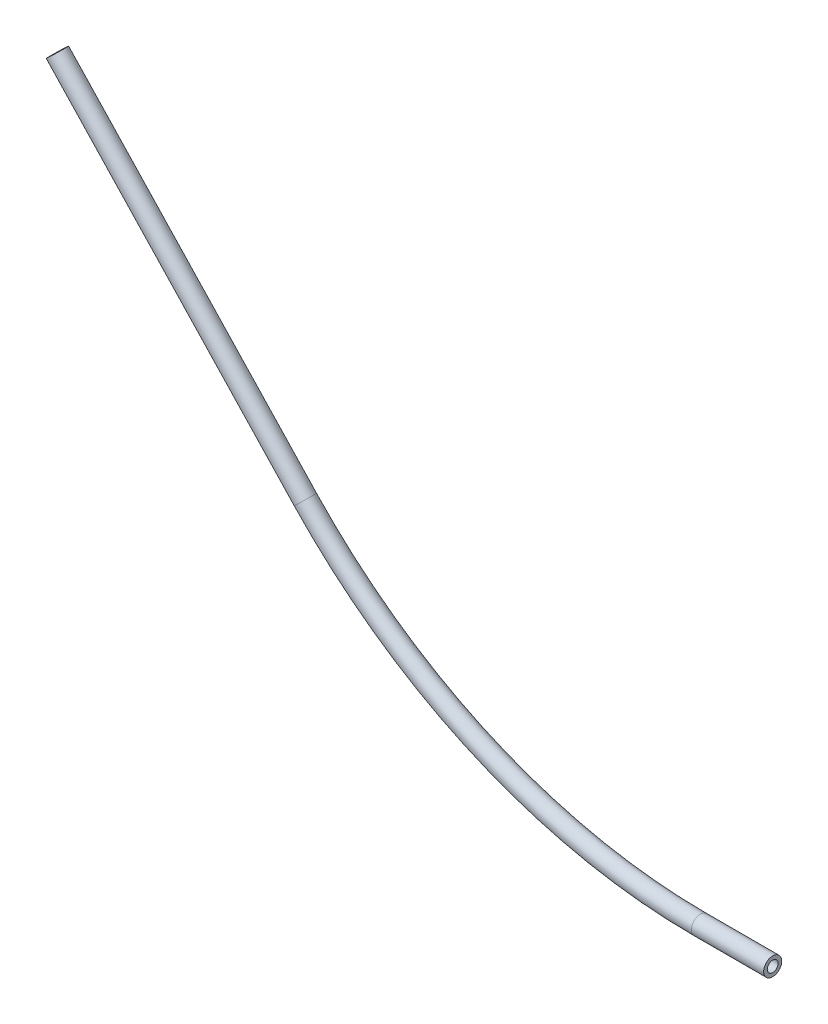
SolidWorks part; units mm, degrees
ref_plane "Front Plane" through (0, 0, 0) normal (0, 0, 1) x (1, 0, 0)
ref_plane "Top Plane" through (0, 0, 0) normal (0, 1, 0) x (1, 0, 0)
ref_plane "Right Plane" through (0, 0, 0) normal (1, 0, 0) x (0, 0, -1)
sketch "Sketch1" plane through (0, 0, 0) normal (1, 0, 0) x (0, 0, -1)
  circle A0 centre (0, 0) radius 1.905
  circle A1 centre (0, 0) radius 3.175
  dimension "D1" = 3.81
  dimension "D2" = 6.35
sketch "Sketch2" plane through (0, 0, 0) normal (0, 0, 1) x (1, 0, 0)
  line L0 (0, 0) -> (-25.4, 0)
  line L1 (-164.1109, 59.9261) -> (-251.1601, 152.4)
  arc A0 (-164.1109, 59.9261) -> (-25.4, 0) centre (-25.4, 190.5) ccw
  dimension "D1" = 381
  dimension "D2" = 25.4
  dimension "D3" = 127
  dimension "D4" = 152.4
sweep "Sweep2" add profiles "Sketch1" path "Sketch2"
sketch "Sketch3" plane through (0, 0, 0) normal (0, 0, 1) x (1, 0, 0)
  line L0 (0, 0) -> (0, 50000) construction
